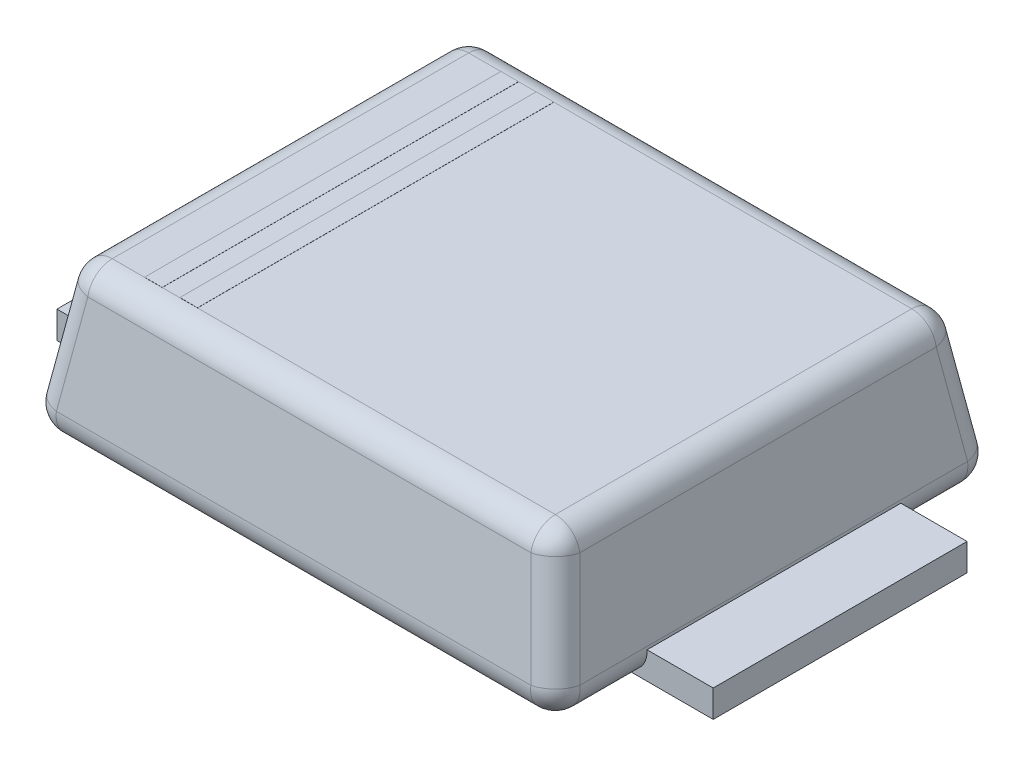
SolidWorks part; units mm, degrees
ref_plane "Front Plane" through (0, 0, 0) normal (0, 0, 1) x (1, 0, 0)
ref_plane "Top Plane" through (0, 0, 0) normal (0, 1, 0) x (1, 0, 0)
ref_plane "Right Plane" through (0, 0, 0) normal (1, 0, 0) x (0, 0, -1)
sketch "Sketch1" plane through (0, 0, 0) normal (0, 1, 0) x (1, 0, 0)
  line L1 (-2.15, 1.8) -> (2.15, 1.8)
  line L2 (-2.15, 1.8) -> (-2.15, -1.8)
  line L3 (-2.15, -1.8) -> (2.15, -1.8)
  line L4 (2.15, 1.8) -> (2.15, -1.8)
  line L5 (-2.15, 1.8) -> (2.15, -1.8) construction
  line L6 (-2.15, -1.8) -> (2.15, 1.8) construction
  point P0 (0, 0)
  dimension "D1" = 4.3
  dimension "D2" = 3.6
extrude "Boss-Extrude1" add sketch "Sketch1" along normal blind 1.2 draft 9
fillet "Fillet1" radius 0.2 12 edges at (0, 1.2, -1.6099) (-1.9599, 1.2, 0) (1.9599, 1.2, 0) (0, 1.2, 1.6099) (-2.055, 0.6, -1.705) (2.055, 0.6, -1.705) (2.055, 0.6, 1.705) (-2.055, 0.6, 1.705) (0, 0, -1.8) (2.15, 0, 0) (-2.15, 0, 0) (0, 0, 1.8)
ref_plane "Plane1" through (0, -0.01, 0) normal (0, -1, 0) x (-1, 0, 0)
sketch "Sketch3" plane through (0, -0.01, 0) normal (0, -1, 0) x (-1, 0, 0)
  line L0 (2.15, 0) -> (-2.15, 0) construction
  line L1 (2.65, -1.025) -> (1.65, -1.025)
  line L2 (2.65, -1.025) -> (2.65, 1.025)
  line L3 (2.65, 1.025) -> (1.65, 1.025)
  line L4 (1.65, -1.025) -> (1.65, 1.025)
  line L5 (2.65, -1.025) -> (1.65, 1.025) construction
  line L6 (2.65, 1.025) -> (1.65, -1.025) construction
  line L8 (-1.65, 1.025) -> (-2.65, 1.025)
  line L9 (-1.65, 1.025) -> (-1.65, -1.025)
  line L10 (-1.65, -1.025) -> (-2.65, -1.025)
  line L11 (-2.65, 1.025) -> (-2.65, -1.025)
  line L12 (-1.65, 1.025) -> (-2.65, -1.025) construction
  line L13 (-1.65, -1.025) -> (-2.65, 1.025) construction
  point P0 (2.15, 0)
  point P11 (0, 0)
  point P12 (0, 0)
  dimension "D1" = 5.3
  dimension "D2" = 1
  dimension "D3" = 2.05
extrude "Boss-Extrude2" add sketch "Sketch3" against normal blind 0.22
sketch "Sketch4" plane through (0, 1.2, 0) normal (0, 1, 0) x (1, 0, 0)
  line L0 (1.7891, 1.4391) -> (-1.7891, 1.4391) construction
  line L1 (-1.5285, 1.4391) -> (-1.3858, 1.4391)
  line L2 (-1.5285, 1.4391) -> (-1.5285, -1.4391)
  line L3 (-1.5285, -1.4391) -> (-1.3858, -1.4391)
  line L4 (-1.3858, 1.4391) -> (-1.3858, -1.4391)
  line L5 (-1.7891, -1.4391) -> (1.7891, -1.4391) construction
  line L6 (-1.3858, 1.4391) -> (-1.2432, 1.4391) construction
  line L7 (-1.2432, 1.4391) -> (-1.1006, 1.4391)
  line L8 (-1.2432, 1.4391) -> (-1.2432, -1.4391)
  line L9 (-1.2432, -1.4391) -> (-1.1006, -1.4391)
  line L10 (-1.1006, 1.4391) -> (-1.1006, -1.4391)
extrude "Boss-Extrude3" add sketch "Sketch4" along normal blind 0.001
equation "\"E_body_width\" = 3.6"
equation "\"D_body_length\"= 4.3"
equation "\"e_pad_width\"= 2.05"
equation "\"g_pad_length\"= 1"
equation "\"c_pad_height\"= ( 0.26 + 0.18 ) / 2"
equation "\"HE_end_pin_length\"= 5.3"
equation "\"angle\"= 9"
equation "\"D1@Sketch1\"= \"D_body_length\""
equation "\"D2@Sketch1\"= \"E_body_width\""
equation "\"A_body_height\" = 1.2"
equation "\"D1@Boss-Extrude1\"= \"A_body_height\""
equation "\"D3@Boss-Extrude1\"= \"angle\""
equation "\"D1@Sketch3\"= \"HE_end_pin_length\""
equation "\"D2@Sketch3\" = \"g_pad_length\""
equation "\"D3@Sketch3\"= \"e_pad_width\""
equation "\"D1@Boss-Extrude2\"= \"c_pad_height\""
